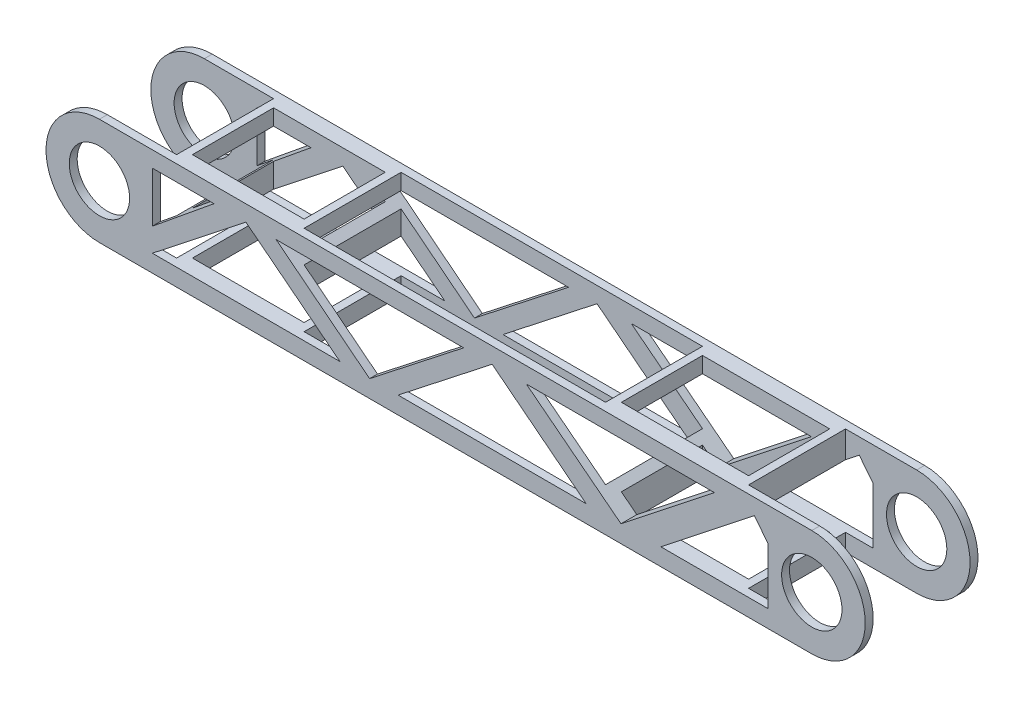
SolidWorks part; units mm, degrees
ref_plane "Alzado" through (0, 0, 0) normal (0, 0, 1) x (1, 0, 0)
ref_plane "Planta" through (0, 0, 0) normal (0, 1, 0) x (1, 0, 0)
ref_plane "Vista lateral" through (0, 0, 0) normal (1, 0, 0) x (0, 0, -1)
sketch "Croquis1" plane through (0, 0, 0) normal (0, 0, 1) x (1, 0, 0)
  line L1 (-180, -35) -> (180, -35)
  line L3 (-180, 35) -> (180, 35)
  arc A0 (-180, 35) -> (-180, -35) centre (-180, 0) ccw
  arc A1 (180, -35) -> (180, 35) centre (180, 0) ccw
  circle A2 centre (-180, 0) radius 15.25
  circle A3 centre (180, 0) radius 15.25
  point P0 (0, 0)
  dimension "D3" = 30.5
  dimension "D4" = 30.5
  dimension "D1" = 360
  dimension "D2" = 70
extrude "Saliente-Extruir1" add sketch "Croquis1" along normal blind 57
sketch "Croquis2" plane through (0, 0, 0) normal (0, 1, 0) x (1, 0, 0)
  line L0 (-215, 0) -> (-215, -57) construction
  line L1 (-215, -50.5) -> (-145, -50.5)
  line L2 (-215, -50.5) -> (-215, -6.5)
  line L3 (-215, -6.5) -> (-145, -6.5)
  line L4 (-145, -50.5) -> (-145, -6.5)
  line L5 (-164.75, 0) -> (-195.25, 0) construction
  line L6 (214.0623, -6.5) -> (144.0623, -6.5)
  line L7 (214.0623, -6.5) -> (214.0623, -50.5)
  line L8 (214.0623, -50.5) -> (144.0623, -50.5)
  line L9 (144.0623, -6.5) -> (144.0623, -50.5)
  line L10 (-80.5581, -6.5) -> (71.7659, -6.5)
  line L11 (-80.5581, -6.5) -> (-80.5581, -50.5)
  line L12 (-80.5581, -50.5) -> (71.7659, -50.5)
  line L13 (71.7659, -6.5) -> (71.7659, -50.5)
  line L14 (180, -57) -> (-180, -57) construction
  line L15 (180, 0) -> (-180, 0) construction
  line L16 (180, -57) -> (215, -57) construction
  point P22 (214.0623, -28.5)
  dimension "D1" = 6.5
  dimension "D2" = 6.5
  dimension "D3" = 6.5
  dimension "D4" = 6.5
  dimension "D5" = 6.5
  dimension "D6" = 6.5
  dimension "D7" = 70
  dimension "D8" = 70
extrude "Cortar-Extruir1" cut sketch "Croquis2" against normal mid plane 80
sketch "Croquis3" plane through (0, 0, 0) normal (0, 0, 1) x (1, 0, 0)
  line L10 (-180, -27) -> (180, -27)
  line L11 (180, 27) -> (-180, 27)
  line L12 (-180, -27) -> (180, -27)
  line L13 (180, 27) -> (-180, 27)
  line L19 (-180, -35) -> (180, -35)
  line L20 (180, 35) -> (-180, 35)
  line L21 (-180, -35) -> (180, -35)
  line L22 (180, 35) -> (-180, 35)
  arc A7 (180, -27) -> (180, 27) centre (180, 0) ccw
  arc A8 (-180, 27) -> (-180, -27) centre (-180, 0) ccw
  arc A9 (180, -27) -> (180, 27) centre (180, 0) ccw
  arc A10 (-180, 27) -> (-180, -27) centre (-180, 0) ccw
  arc A16 (180, -35) -> (180, 35) centre (180, 0) ccw
  arc A17 (-180, 35) -> (-180, -35) centre (-180, 0) ccw
  arc A18 (180, -35) -> (180, 35) centre (180, 0) ccw
  arc A19 (-180, 35) -> (-180, -35) centre (-180, 0) ccw
  dimension "D1" = 8
  dimension "D2" = 0
extrude "Cortar-Extruir3" cut sketch "Croquis3" against normal mid plane 150
sketch "Croquis4" plane through (0, 0, 6.5) normal (0, 0, 1) x (1, 0, 0)
  line L0 (-145, 27) -> (-180, 27)
  line L1 (-145, 27) -> (-145, -27)
  line L2 (-145, -27) -> (-180, -27)
  circle A0 centre (-180, 0) radius 15.25
  arc A1 (-180, 27) -> (-180, -27) centre (-180, 0) ccw
extrude "Cortar-Extruir4" cut sketch "Croquis4" against normal blind 2.5
sketch "Croquis5" plane through (0, 0, 50.5) normal (0, 0, -1) x (-1, 0, 0)
  line L0 (180, 27) -> (145, 27)
  line L1 (145, 27) -> (145, -27)
  line L2 (145, -27) -> (180, -27)
  circle A0 centre (180, 0) radius 15.25
  arc A1 (180, -27) -> (180, 27) centre (180, 0) ccw
extrude "Cortar-Extruir5" cut sketch "Croquis5" against normal blind 2.5
sketch "Croquis6" plane through (0, 0, 6.5) normal (0, 0, 1) x (1, 0, 0)
  line L0 (180, 27) -> (144.0623, 27)
  line L1 (144.0623, 27) -> (144.0623, -27)
  line L2 (144.0623, -27) -> (180, -27)
  circle A0 centre (180, 0) radius 15.0836
  arc A1 (180, -27) -> (180, 27) centre (180, 0) ccw
extrude "Cortar-Extruir6" cut sketch "Croquis6" against normal blind 2.5
sketch "Croquis7" plane through (0, 0, 50.5) normal (0, 0, -1) x (-1, 0, 0)
  line L0 (-180, -27) -> (-144.0623, -27)
  line L1 (-144.0623, -27) -> (-144.0623, 27)
  line L2 (-144.0623, 27) -> (-180, 27)
  arc A0 (-180, 27) -> (-180, -27) centre (-180, 0) ccw
  circle A1 centre (-180, 0) radius 15.25
extrude "Cortar-Extruir7" cut sketch "Croquis7" against normal blind 2.5
sketch "Croquis8" plane through (0, 0, 50.5) normal (0, 0, -1) x (-1, 0, 0)
  line L0 (-71.7659, 27) -> (80.5581, 27)
  line L1 (80.5581, 27) -> (80.5581, -27)
  line L2 (80.5581, -27) -> (-71.7659, -27)
  line L3 (-71.7659, -27) -> (-71.7659, 27)
extrude "Cortar-Extruir8" cut sketch "Croquis8" against normal blind 2.5
sketch "Croquis9" plane through (0, 0, 6.5) normal (0, 0, 1) x (1, 0, 0)
  line L0 (71.7659, -27) -> (71.7659, 27)
  line L1 (71.7659, 27) -> (-80.5581, 27)
  line L2 (-80.5581, 27) -> (-80.5581, -27)
  line L3 (-80.5581, -27) -> (71.7659, -27)
extrude "Cortar-Extruir9" cut sketch "Croquis9" against normal blind 2.5
sketch "Croquis10" plane through (0, 27, 0) normal (0, 1, 0) x (1, 0, 0)
  line L0 (-141, -8) -> (-141, -49)
  line L1 (-141, -49) -> (-84.5581, -49)
  line L2 (-84.5581, -49) -> (-84.5581, -8)
  line L4 (-141, -8) -> (-84.5581, -8)
extrude "Cortar-Extruir10" cut sketch "Croquis10" against normal blind 70
sketch "Croquis11" plane through (0, 27, 0) normal (0, 1, 0) x (1, 0, 0)
  line L0 (75.7659, -8) -> (75.7659, -49)
  line L1 (75.7659, -49) -> (140.0623, -49)
  line L2 (140.0623, -49) -> (140.0623, -8)
  line L4 (75.7659, -8) -> (140.0623, -8)
extrude "Cortar-Extruir11" cut sketch "Croquis11" against normal blind 70
sketch "Croquis12" plane through (0, 0, 57) normal (0, 0, 1) x (1, 0, 0)
  line L0 (-153.2467, -18.2608) -> (-105.9804, 18.9839)
  line L1 (-153.2467, 18.9839) -> (-122.113, 18.9839)
  line L2 (-153.2467, 18.9839) -> (-153.2467, -6.4414)
  line L3 (-153.2467, -18.2608) -> (-58.4469, -18.2608)
  line L4 (157.8311, 10.3041) -> (157.8311, -18.2608)
  line L5 (-105.9804, 18.9839) -> (-58.4469, -18.2608)
  line L6 (-153.2467, -6.4414) -> (-122.113, 18.9839)
  line L7 (-90.7121, 18.9839) -> (-43.4667, -18.2608)
  line L8 (-43.4667, -18.2608) -> (4.0669, 18.9839)
  line L9 (-29.0626, -18.2608) -> (18.471, 18.9839)
  line L10 (18.471, 18.9839) -> (66.0045, -18.2608)
  line L11 (35.7559, 18.9839) -> (83.5775, -18.2608)
  line L12 (83.5775, -18.2608) -> (130.8229, 18.9839)
  line L13 (103.7432, -18.2608) -> (150.9886, 18.9839)
  line L14 (150.9886, 18.9839) -> (157.8311, 10.3041)
  line L15 (-90.7121, 18.9839) -> (4.0669, 18.9839)
  line L16 (-29.0626, -18.2608) -> (66.0045, -18.2608)
  line L17 (35.7559, 18.9839) -> (130.8229, 18.9839)
  line L18 (103.7432, -18.2608) -> (157.8311, -18.2608)
extrude "Cortar-Extruir12" cut sketch "Croquis12" against normal blind 78
